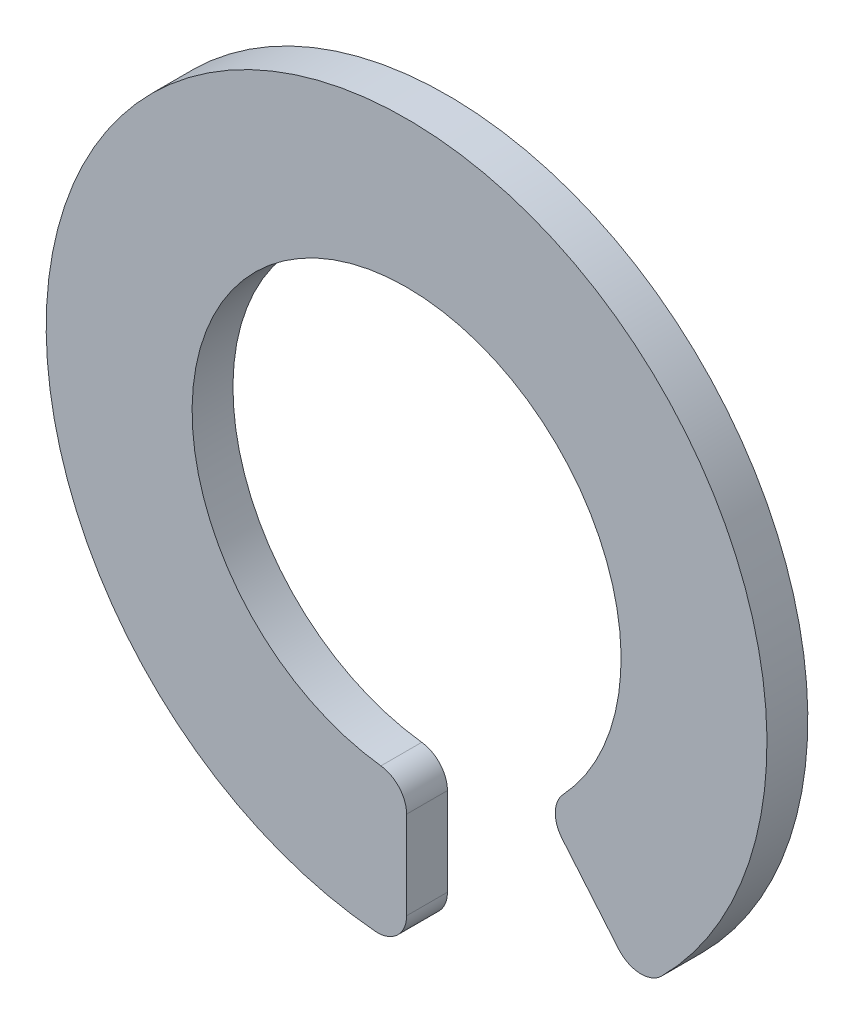
SolidWorks part; units mm, degrees
material "Acier allié inoxydable"
ref_plane "Plan de face" through (0, 0, 0) normal (0, 0, 1) x (1, 0, 0)
ref_plane "Plan de dessus" through (0, 0, 0) normal (0, 1, 0) x (1, 0, 0)
ref_plane "Plan de droite" through (0, 0, 0) normal (1, 0, 0) x (0, 0, -1)
sketch "Esquisse1" plane through (0, 0, 0) normal (0, 0, 1) x (1, 0, 0)
  line L0 (0, -1.47) -> (0, -2.47)
  line L1 (0.9449, -1.1261) -> (1.5877, -1.8921)
  line L2 (0, -1.47) -> (0, 0) construction
  line L3 (0, 0) -> (0.9449, -1.1261) construction
  arc A0 (0.9449, -1.1261) -> (0, -1.47) centre (0, 0) ccw
  arc A1 (1.5877, -1.8921) -> (0, -2.47) centre (0, 0) ccw
  dimension "D1" = 2.94
  dimension "D2" = 1
  dimension "D3" = 40
extrude "Boss.-Extru.1" add sketch "Esquisse1" along normal blind 0.28
fillet "Congé1" radius 0.2 4 edges at (1.5877, -1.8921, 0.14) (0.9449, -1.1261, 0.14) (0, -2.47, 0.14) (0, -1.47, 0.14)
